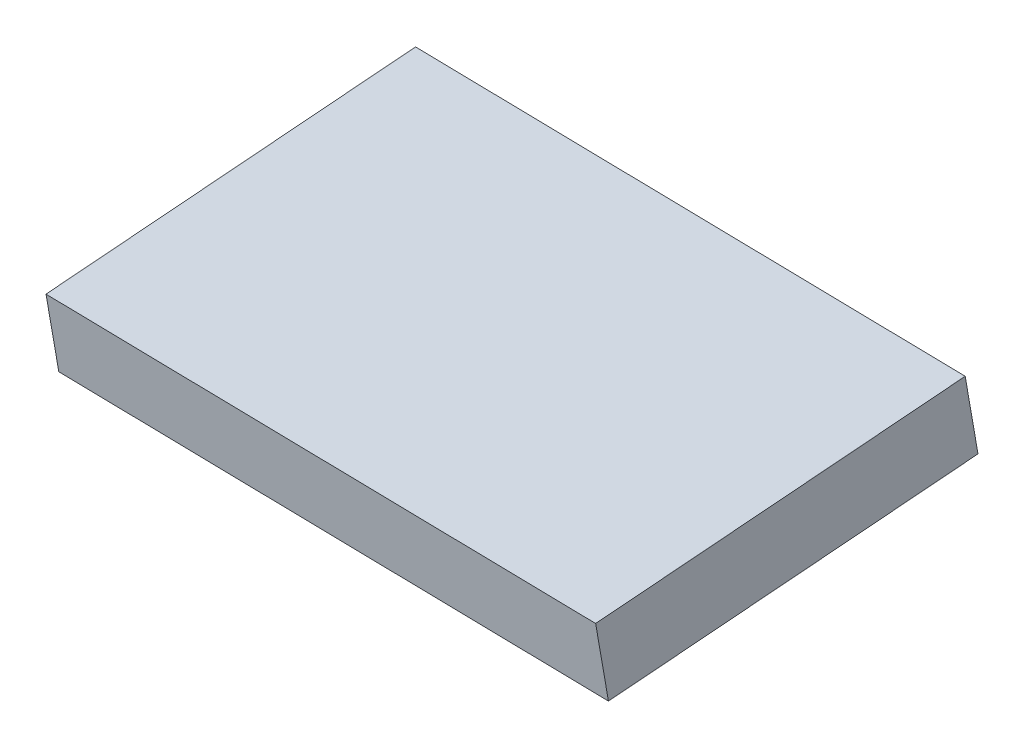
SolidWorks part; units mm, degrees
material "AISI 4130 Steel, normalized at 870C"
ref_plane "Top" through (0, 0, 0) normal (0, 0, 1) x (1, 0, 0)
ref_plane "Right" through (0, 0, 0) normal (0, 1, 0) x (1, 0, 0)
ref_plane "Front" through (0, 0, 0) normal (1, 0, 0) x (0, 0, -1)
sketch "Sketch2" plane through (-24.5806, 506.9994, 67.9069) normal (0.048, -0.99, -0.1326) x (-0.9988, -0.0476, -0.0064)
  line L0 (-31.1308, -50.7832) -> (-18.5751, -50.1238)
  line L1 (-18.5751, -50.1238) -> (-18.1755, -57.7333)
  line L2 (-18.5751, -50.1238) -> (-17.6206, -68.2977) construction
  line L3 (-18.1755, -57.7333) -> (-30.7312, -58.3927)
  line L4 (-31.1308, -50.7832) -> (-30.1763, -68.9571) construction
  line L5 (-30.7312, -58.3927) -> (-31.1308, -50.7832)
  dimension "D1" = 7.62
extrude "Boss-Extrude1" add sketch "Sketch2" against normal blind 1.524
